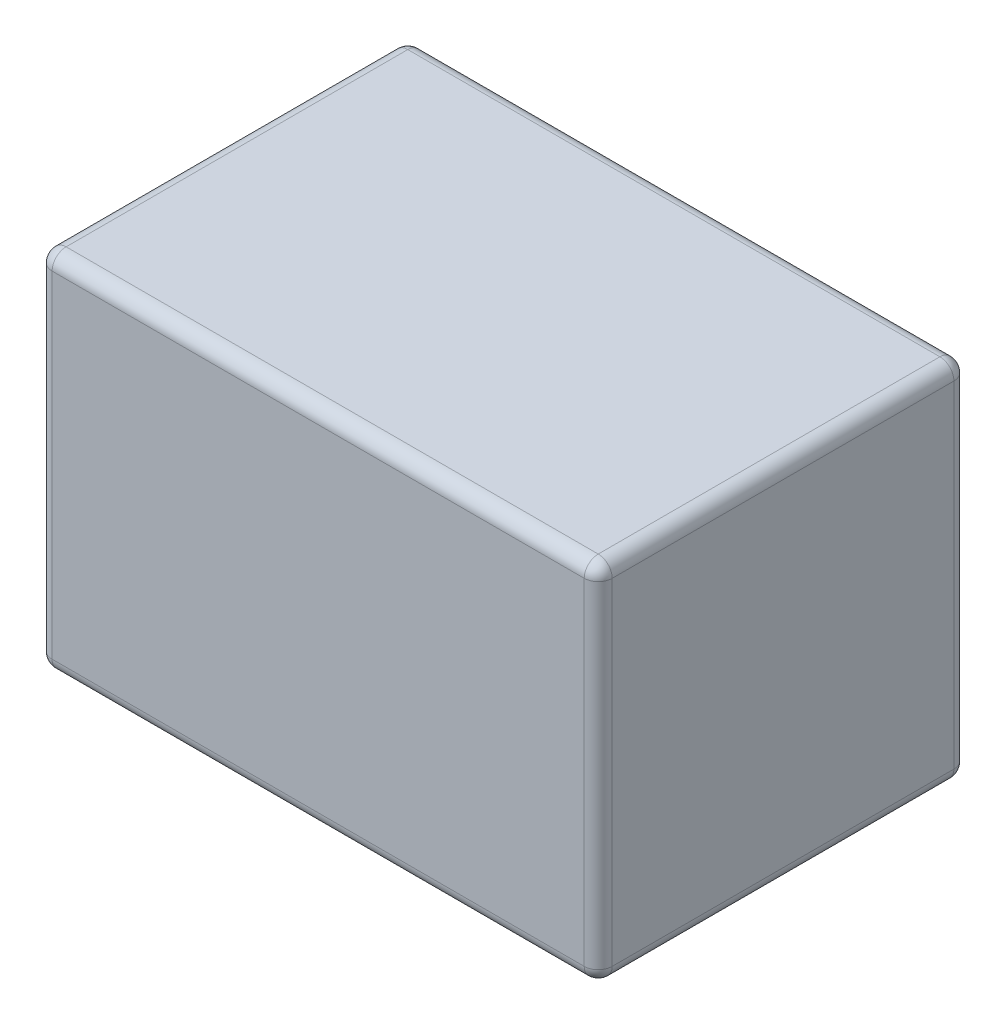
SolidWorks part; units mm, degrees
ref_plane "Front Plane" through (0, 0, 0) normal (0, 0, 1) x (1, 0, 0)
ref_plane "Top Plane" through (0, 0, 0) normal (0, 1, 0) x (1, 0, 0)
ref_plane "Right Plane" through (0, 0, 0) normal (1, 0, 0) x (0, 0, -1)
sketch "Sketch1" plane through (0, 0, 0) normal (0, 0, 1) x (1, 0, 0)
  line L0 (-68.5656, 45.3225) -> (131.4344, 45.3225)
  line L1 (131.4344, 45.3225) -> (131.4344, -84.6775)
  line L2 (131.4344, -84.6775) -> (-68.5656, -84.6775)
  line L3 (-68.5656, 45.3225) -> (-68.5656, -84.6775)
  point P2 (131.4344, -19.6775)
  point P5 (131.4344, -3.1425)
  point P6 (131.4344, -36.2125)
  dimension "D1" = 200
  dimension "D2" = 130
  dimension "D3" = 16.535
  dimension "D4" = 16.535
extrude "Boss-Extrude1" add sketch "Sketch1" along normal blind 132
fillet "Fillet1" radius 5 12 edges at (31.4344, -84.6775, 0) (-68.5656, -84.6775, 66) (-68.5656, -19.6775, 0) (-68.5656, 45.3225, 66) (31.4344, 45.3225, 0) (131.4344, -84.6775, 66) (131.4344, 45.3225, 66) (131.4344, -19.6775, 0) (131.4344, -19.6775, 132) (31.4344, -84.6775, 132) (-68.5656, -19.6775, 132) (31.4344, 45.3225, 132)
sketch "Sketch2" plane through (0, 0, 0) normal (0, 0, -1) x (-1, 0, 0)
  line L1 (-126.4344, 40.3225) -> (-126.4344, -79.6775)
  line L2 (-126.4344, -79.6775) -> (63.5656, -79.6775)
  line L3 (63.5656, -79.6775) -> (63.5656, 40.3225)
  line L4 (63.5656, 40.3225) -> (-126.4344, 40.3225)
  circle A0 centre (-31.4344, -19.6775) radius 0.25
  point P0 (-31.4344, -19.6775)
  dimension "D3" = 0.5
  dimension "D1" = 60
  dimension "D2" = 95
extrude "Boss-Extrude2" add sketch "Sketch2" along normal blind 0.5 contours L4 L1 L2 L3
